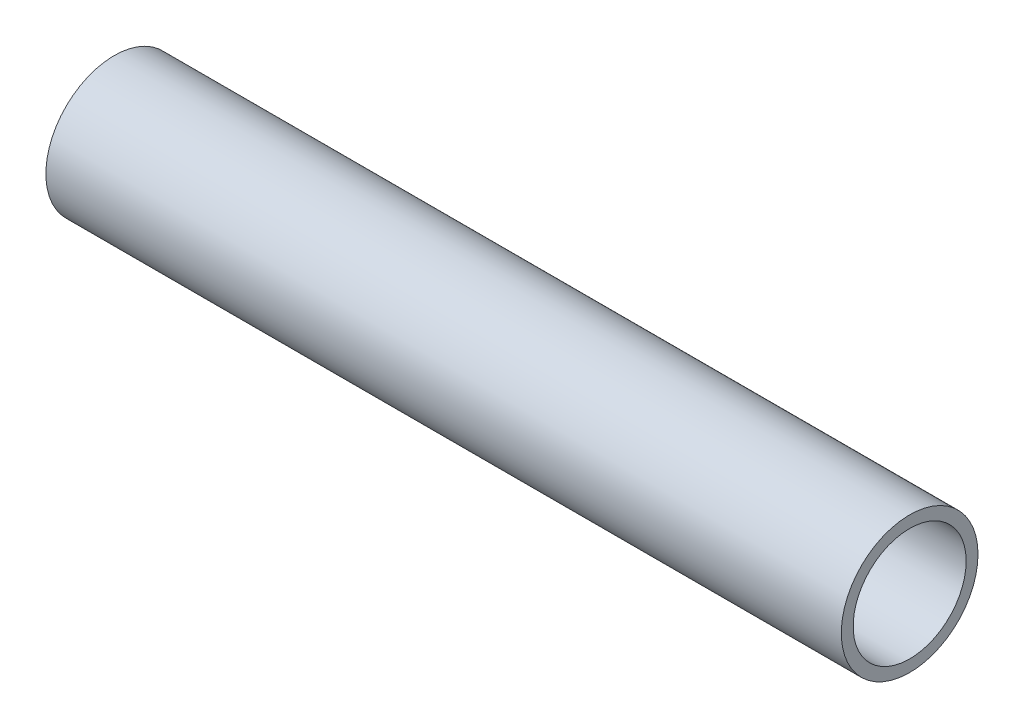
SolidWorks part; units mm, degrees
material "6061 Alloy"
ref_plane "Front Plane" through (0, 0, 0) normal (0, 0, 1) x (1, 0, 0)
ref_plane "Top Plane" through (0, 0, 0) normal (0, 1, 0) x (1, 0, 0)
ref_plane "Right Plane" through (0, 0, 0) normal (1, 0, 0) x (0, 0, -1)
sketch "Sketch1" plane through (0, 0, 0) normal (1, 0, 0) x (0, 0, -1)
  circle A0 centre (0, 0) radius 9.525
  circle A1 centre (0, 0) radius 7.874
  dimension "D1" = 19.05
  dimension "D2" = 15.748
extrude "Boss-Extrude1" add sketch "Sketch1" along normal mid plane 110.8456
